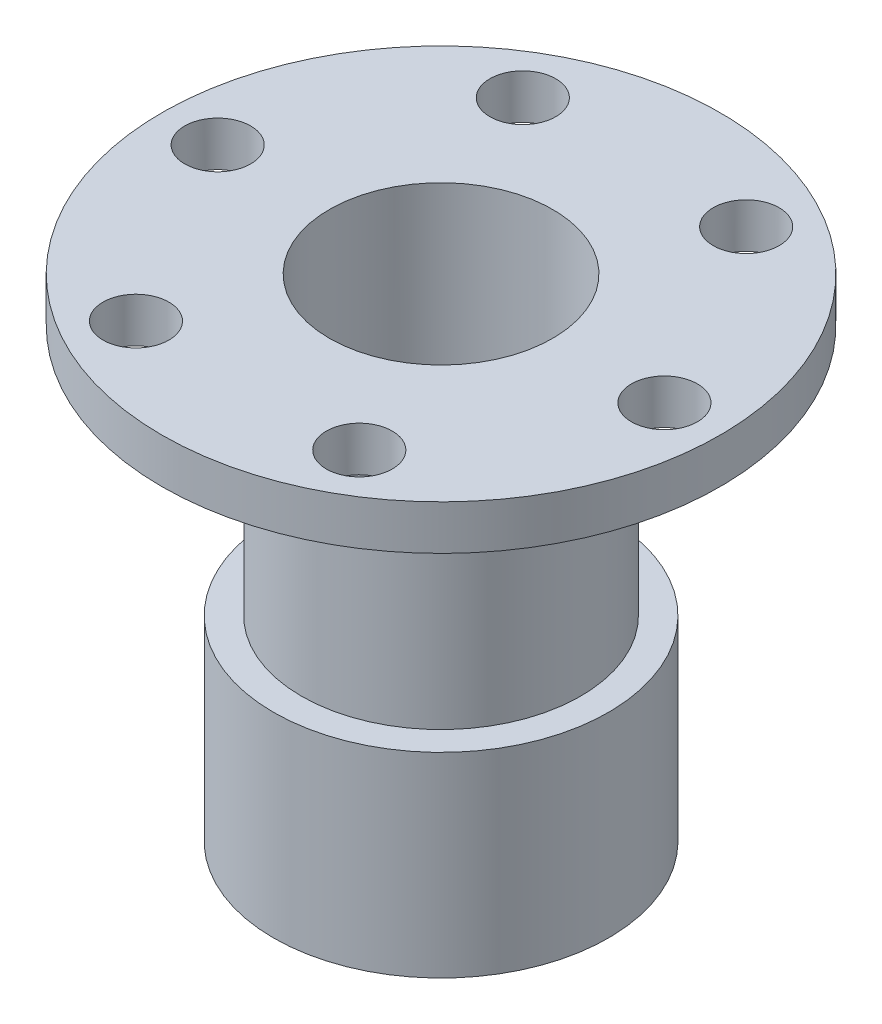
SolidWorks part; units mm, degrees
ref_plane "Front Plane" through (0, 0, 0) normal (0, 0, 1) x (1, 0, 0)
ref_plane "Top Plane" through (0, 0, 0) normal (0, 1, 0) x (1, 0, 0)
ref_plane "Right Plane" through (0, 0, 0) normal (1, 0, 0) x (0, 0, -1)
sketch "Sketch2" plane through (0, 0, 0) normal (0, 1, 0) x (1, 0, 0)
  circle A0 centre (0, 0) radius 30
  dimension "D1" = 60
extrude "Boss-Extrude1" add sketch "Sketch2" along normal blind 35
sketch "Sketch3" plane through (0, 35, 0) normal (0, 1, 0) x (1, 0, 0)
  circle A0 centre (0, 0) radius 25
  dimension "D1" = 50
extrude "Boss-Extrude2" add sketch "Sketch3" along normal blind 45
sketch "Sketch4" plane through (0, 80, 0) normal (0, 1, 0) x (1, 0, 0)
  circle A0 centre (0, 0) radius 50
  dimension "D1" = 100
extrude "Boss-Extrude3" add sketch "Sketch4" along normal blind 8
sketch "Sketch5" plane through (0, 0, 0) normal (0, -1, 0) x (1, 0, 0)
  circle A0 centre (0, 0) radius 25
  dimension "D1" = 50
extrude "Cut-Extrude1" cut sketch "Sketch5" against normal blind 25
sketch "Sketch6" plane through (0, 88, 0) normal (0, 1, 0) x (1, 0, 0)
  circle A0 centre (0, 0) radius 20
  dimension "D1" = 40
extrude "Cut-Extrude2" cut sketch "Sketch6" against normal up to next
sketch "Sketch7" plane through (0, 88, 0) normal (0, 1, 0) x (1, 0, 0)
  circle A0 centre (0, 0) radius 40 construction
  circle A1 centre (40, 0) radius 5.9
  dimension "D1" = 80
  dimension "D2" = 11.8
extrude "Cut-Extrude3" cut sketch "Sketch7" against normal blind 40
pattern_circular "CirPattern1" count 6 over 360 about axis through (0, 0, 0) along (0, 1, 0) of "Cut-Extrude3"
